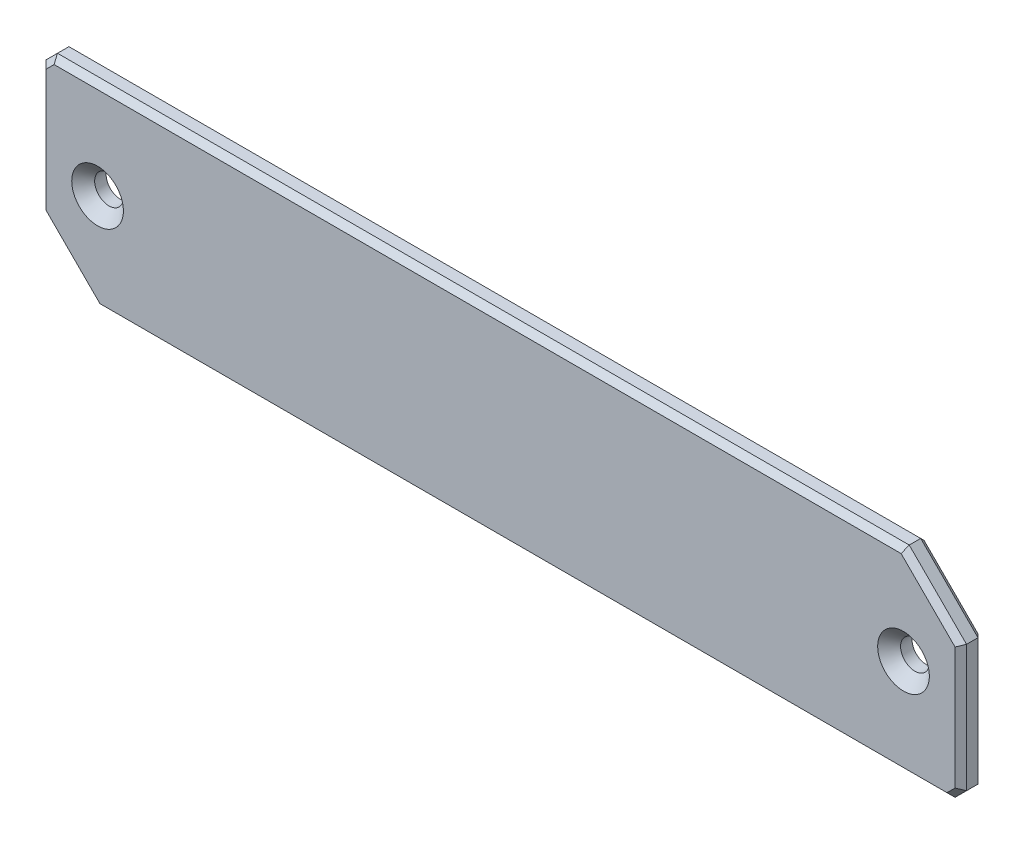
SolidWorks part; units mm, degrees
ref_plane "前视基准面" through (0, 0, 0) normal (0, 0, 1) x (1, 0, 0)
ref_plane "上视基准面" through (0, 0, 0) normal (0, 1, 0) x (1, 0, 0)
ref_plane "右视基准面" through (0, 0, 0) normal (1, 0, 0) x (0, 0, -1)
sketch "草图1" plane through (0, 0, 0) normal (0, 0, 1) x (1, 0, 0)
  line L0 (-65.8599, 17.8844) -> (-64.8599, 18.8844)
  line L1 (-64.8599, 18.8844) -> (9.4543, 18.8844)
  line L2 (-65.8599, 17.8844) -> (-65.8599, 6.8177)
  line L3 (-60.8599, 1.8177) -> (13.4543, 1.8177)
  line L4 (14.4543, 13.8844) -> (14.4543, 2.8177)
  line L5 (14.4543, 2.8177) -> (13.4543, 1.8177)
  line L6 (9.4543, 18.8844) -> (14.4543, 13.8844)
  line L7 (-65.8599, 6.8177) -> (-60.8599, 1.8177)
  circle A0 centre (-60.8599, 10.3511) radius 1.2549
  circle A1 centre (9.4543, 10.3511) radius 1.2549
  point P0 (-65.8599, 18.8844)
  point P1 (14.4543, 1.8177)
  point P2 (-65.8599, 1.8177)
  point P3 (14.4543, 18.8844)
  dimension "D1" = 5
  dimension "D2" = 5
extrude "凸台-拉伸1" add sketch "草图1" along normal blind 2
chamfer "倒角1" distance 1 angle 45 2 edges at (10.7092, 10.3511, 2) (-59.605, 10.3511, 2)
chamfer "倒角3" distance 0.5 angle 45 8 edges at (-65.3599, 18.3844, 2) (-65.8599, 12.3511, 2) (-63.3599, 4.3177, 2) (-23.7028, 1.8177, 2) (13.9543, 2.3177, 2) (14.4543, 8.3511, 2) (-27.7028, 18.8844, 2) (11.9543, 16.3844, 2)
chamfer "倒角4" distance 0.5 angle 45 8 edges at (11.9543, 16.3844, 0) (14.4543, 8.3511, 0) (13.9543, 2.3177, 0) (-23.7028, 1.8177, 0) (-63.3599, 4.3177, 0) (-65.8599, 12.3511, 0) (-65.3599, 18.3844, 0) (-27.7028, 18.8844, 0)
sketch "草图2" plane through (0, 0, 2) normal (0, 0, 1) x (1, 0, 0)
  line L0 (9.2472, 18.3844) -> (-64.6528, 18.3844) construction
  line L1 (-56.8599, 17.3844) -> (5.4543, 17.3844)
  line L2 (-56.8599, 17.3844) -> (-56.8599, 3.3177)
  line L3 (-56.8599, 3.3177) -> (5.4543, 3.3177)
  line L4 (5.4543, 17.3844) -> (5.4543, 3.3177)
  line L6 (-60.6528, 2.3177) -> (13.2472, 2.3177) construction
  circle A0 centre (-60.8599, 10.3511) radius 2.2549 construction
  circle A1 centre (9.4543, 10.3511) radius 2.2549 construction
  dimension "D5" = 14.0668
  dimension "D1" = 1
  dimension "D2" = 1
  dimension "D3" = 4
  dimension "D4" = 4
